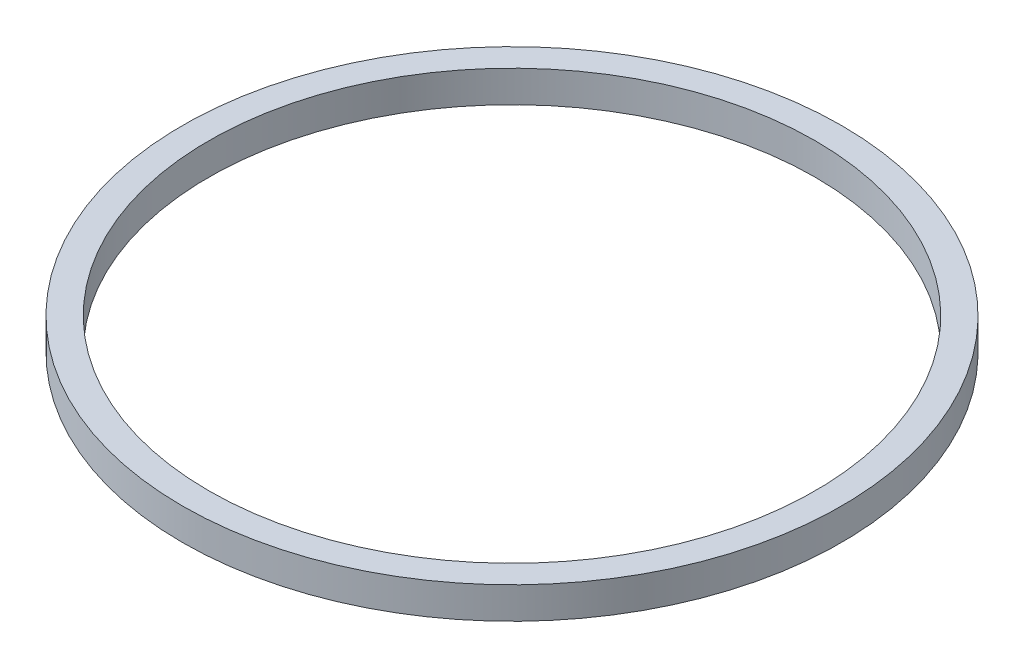
SolidWorks part; units mm, degrees
ref_plane "前视基准面" through (0, 0, 0) normal (0, 0, 1) x (1, 0, 0)
ref_plane "上视基准面" through (0, 0, 0) normal (0, 1, 0) x (1, 0, 0)
ref_plane "右视基准面" through (0, 0, 0) normal (1, 0, 0) x (0, 0, -1)
other "Configuration Table"
sketch "草图1" plane through (0, 0, 0) normal (0, 1, 0) x (1, 0, 0)
  circle A0 centre (0, 0) radius 57.5
  circle A1 centre (0, 0) radius 62.5
  dimension "D1" = 115
  dimension "D2" = 125
extrude "凸台-拉伸1" add sketch "草图1" along normal blind 6
